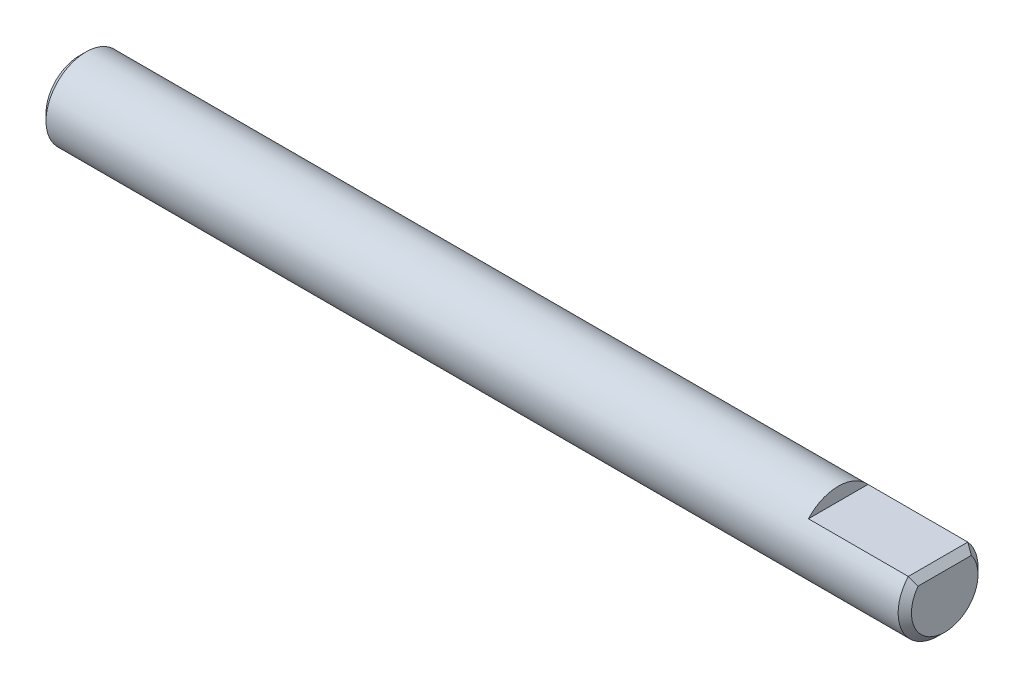
SolidWorks part; units mm, degrees
ref_plane "Front Plane" through (0, 0, 0) normal (0, 0, 1) x (1, 0, 0)
ref_plane "Top Plane" through (0, 0, 0) normal (0, 1, 0) x (1, 0, 0)
ref_plane "Right Plane" through (0, 0, 0) normal (1, 0, 0) x (0, 0, -1)
sketch "Sketch1" plane through (0, 0, 0) normal (1, 0, 0) x (0, 0, -1)
  circle A0 centre (0, 0) radius 3
  dimension "D1" = 6
extrude "Boss-Extrude1" add sketch "Sketch1" along normal mid plane 65
sketch "Sketch2" plane through (32.5, 0, 0) normal (1, 0, 0) x (0, 0, -1)
  line L0 (-2.2361, 2) -> (2.2361, 2)
  circle A1 centre (0, 0) radius 3
  arc A2 (2.2361, 2) -> (-2.2361, 2) centre (0, 0) ccw
  dimension "D2" = 2
  dimension "D1" = 0
extrude "Cut-Extrude1" cut sketch "Sketch2" against normal blind 8
chamfer "Chamfer1" distance 0.5 angle 45 3 edges at (-32.5, 0, -3) (32.5, -3, 0) (32.5, 2, 0)
